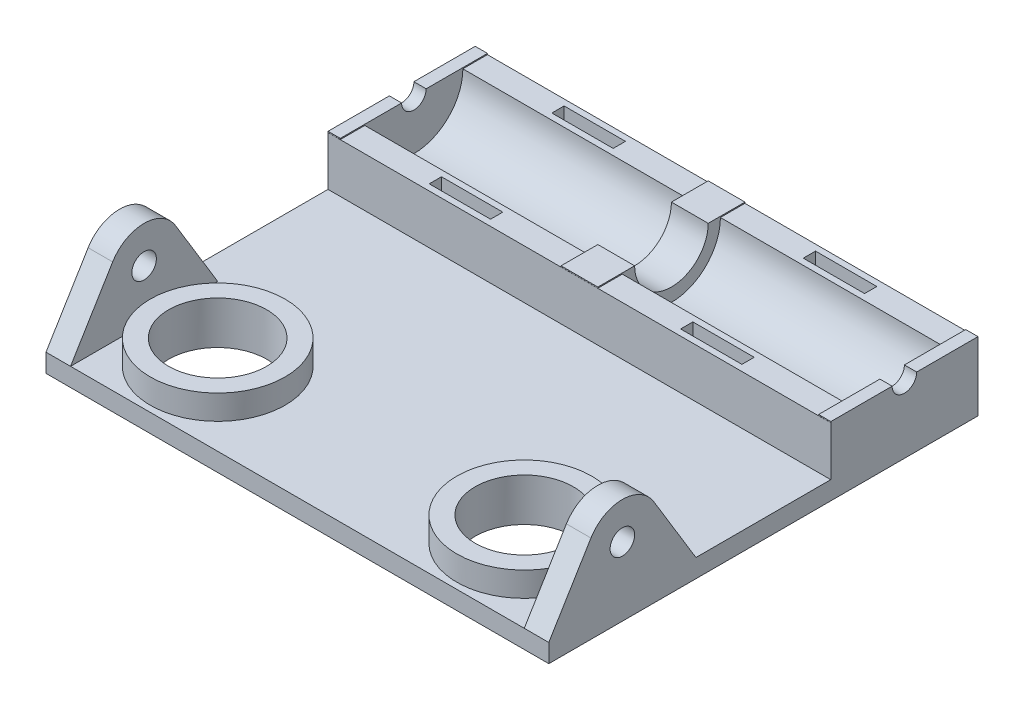
SolidWorks part; units mm, degrees
ref_plane "Front Plane" through (0, 0, 0) normal (0, 0, 1) x (1, 0, 0)
ref_plane "Top Plane" through (0, 0, 0) normal (0, 1, 0) x (1, 0, 0)
ref_plane "Right Plane" through (0, 0, 0) normal (1, 0, 0) x (0, 0, -1)
sketch "Sketch1" plane through (0, 0, 0) normal (0, 1, 0) x (1, 0, 0)
  line L1 (-20.5, -17.5) -> (20.5, -17.5)
  line L2 (-20.5, -17.5) -> (-20.5, 17.5)
  line L3 (-20.5, 17.5) -> (20.5, 17.5)
  line L4 (20.5, -17.5) -> (20.5, 17.5)
  line L5 (-20.5, -17.5) -> (20.5, 17.5) construction
  line L6 (-20.5, 17.5) -> (20.5, -17.5) construction
  point P0 (0, 0)
  dimension "D1" = 41
  dimension "D2" = 35
extrude "Boss-Extrude1" add sketch "Sketch1" along normal blind 1.5
sketch "Sketch2" plane through (20.5, 0, 0) normal (1, 0, 0) x (0, 0, -1)
  line L0 (15.5, 5.6) -> (17.5, 5.6)
  line L1 (17.5, 5.6) -> (17.5, 1.5)
  line L2 (7.5, 5.6) -> (5.5, 5.6)
  line L3 (5.5, 5.6) -> (5.5, 1.5)
  line L4 (-17.5, 1.5) -> (17.5, 1.5) construction
  line L5 (5.5, 1.5) -> (17.5, 1.5)
  arc A0 (7.5, 5.6) -> (15.5, 5.6) centre (11.5, 5.6) ccw
  dimension "D3" = 8
  dimension "D4" = 4.1
  dimension "D1" = 2
  dimension "D2" = 2
sketch "Sketch3" plane through (0, 0, 0) normal (1, 0, 0) x (0, 0, -1)
  line L0 (5.5, 1.5) -> (5.5, 5.6)
  line L1 (5.5, 5.6) -> (8.5, 5.6)
  line L2 (17.5, 5.6) -> (17.5, 1.5)
  line L3 (17.5, 1.5) -> (17.5, 0) construction
  line L4 (17.5, 1.5) -> (5.5, 1.5)
  line L5 (14.5, 5.6) -> (17.5, 5.6)
  arc A0 (8.5, 5.6) -> (14.5, 5.6) centre (11.5, 5.6) ccw
  dimension "D1" = 6
extrude "Boss-Extrude3" add sketch "Sketch3" along normal mid plane 3
sketch "Sketch4" plane through (-20.5, 0, 0) normal (-1, 0, 0) x (0, 0, 1)
  line L0 (-10.5, 5.6) -> (-5.5, 5.6)
  line L1 (-17.5, 5.6) -> (-12.5, 5.6)
  line L2 (-17.5, 5.6) -> (-17.5, 1.5)
  line L3 (-17.5, 1.5) -> (-5.5, 1.5)
  line L4 (-5.5, 5.6) -> (-5.5, 1.5)
  arc A0 (-12.5, 5.6) -> (-10.5, 5.6) centre (-11.5, 5.6) ccw
  dimension "D1" = 2
extrude "Boss-Extrude4" add sketch "Sketch4" against normal blind 1
mirror "Mirror1" about plane through (0, 0, 0) normal (1, 0, 0) of "Boss-Extrude4"
sketch "Sketch5" plane through (-20.5, 0, 0) normal (-1, 0, 0) x (0, 0, 1)
  line L0 (8.9359, 7.1573) -> (5.5, 1.5)
  line L1 (-5.5, 1.5) -> (17.5, 1.5) construction
  line L2 (14.0641, 7.1573) -> (17.5, 1.5)
  line L3 (5.5, 1.5) -> (17.5, 1.5)
  line L5 (-10.5, 5.6) -> (-5.5, 5.6) construction
  circle A0 centre (11.5, 5.6) radius 1
  arc A1 (14.0641, 7.1573) -> (8.9359, 7.1573) centre (11.5, 5.6) ccw
  dimension "D1" = 2
  dimension "D2" = 6
  dimension "D3" = 0
  dimension "D4" = 6
  dimension "D5" = 12
extrude "Boss-Extrude5" add sketch "Sketch5" against normal blind 2
mirror "Mirror2" about plane through (0, 0, 0) normal (1, 0, 0) of "Boss-Extrude5"
sketch "Sketch6" plane through (0, 1.5, 0) normal (0, 1, 0) x (1, 0, 0)
  line L0 (-18.5, -17.5) -> (18.5, -17.5) construction
  line L1 (-20.5, -17.5) -> (-20.5, -14.0641) construction
  line L2 (20.5, -17.5) -> (20.5, -14.0641) construction
  circle A0 centre (-12.5, -11.5) radius 4
  circle A1 centre (12.5, -11.5) radius 4
  dimension "D1" = 8
  dimension "D2" = 8
  dimension "D3" = 6
  dimension "D4" = 6
  dimension "D5" = 8
  dimension "D6" = 8
extrude "Cut-Extrude1" cut sketch "Sketch6" against normal blind 3
sketch "Sketch7" plane through (0, 1.5, 0) normal (0, 1, 0) x (1, 0, 0)
  circle A0 centre (12.5, -11.5) radius 4 construction
  circle A1 centre (-12.5, -11.5) radius 4 construction
  circle A2 centre (12.5, -11.5) radius 4
  circle A3 centre (-12.5, -11.5) radius 4
  circle A4 centre (-12.5, -11.5) radius 5.5
  circle A5 centre (12.5, -11.5) radius 5.5
  dimension "D1" = 1.5
  dimension "D2" = 1.5
extrude "Boss-Extrude6" add sketch "Sketch7" along normal blind 2
sketch "Sketch8" plane through (0, 5.6, 0) normal (0, 1, 0) x (1, 0, 0)
  line L1 (-12.75, 17) -> (-7.75, 17)
  line L2 (-12.75, 17) -> (-12.75, 16)
  line L3 (-12.75, 16) -> (-7.75, 16)
  line L4 (-7.75, 17) -> (-7.75, 16)
  line L5 (20.5, 11.5) -> (-21.9868, 11.5) construction
  line L6 (20.5, 5.5) -> (20.5, 17.5) construction
  line L7 (-7.75, 6) -> (-7.75, 7)
  line L8 (-12.75, 7) -> (-7.75, 7)
  line L9 (-12.75, 6) -> (-12.75, 7)
  line L10 (-12.75, 6) -> (-7.75, 6)
  line L11 (0, 18.4456) -> (0, 2.7509) construction
  line L12 (0, -55) -> (0, 55) construction
  line L13 (12.75, 6) -> (7.75, 6)
  line L14 (12.75, 6) -> (12.75, 7)
  line L15 (12.75, 7) -> (7.75, 7)
  line L16 (7.75, 6) -> (7.75, 7)
  line L17 (-22.5, 17.5) -> (22.5, 17.5) construction
  line L18 (-20.5, 12.5) -> (-20.5, 17.5) construction
  line L20 (7.75, 17) -> (7.75, 16)
  line L21 (12.75, 16) -> (7.75, 16)
  line L22 (12.75, 17) -> (12.75, 16)
  line L23 (12.75, 17) -> (7.75, 17)
  dimension "D1" = 1
  dimension "D2" = 5
  dimension "D3" = 7.75
  dimension "D4" = 0.5
sketch "Sketch9" plane through (0, 0, 0) normal (1, 0, 0) x (0, 0, -1)
  line L0 (15.4936, 5.5137) -> (17.4936, 5.5137)
  line L1 (17.4936, 5.5137) -> (17.4936, 1.4137)
  line L2 (7.4936, 5.5137) -> (5.4936, 5.5137)
  line L3 (5.4936, 5.5137) -> (5.4936, 1.4137)
  line L4 (5.4936, 1.4137) -> (17.4936, 1.4137)
  arc A0 (7.4936, 5.5137) -> (15.4936, 5.5137) centre (11.4936, 5.5137) ccw
  dimension "D3" = 8
  dimension "D1" = 2
  dimension "D2" = 2
extrude "Boss-Extrude7" add sketch "Sketch9" along normal mid plane 41
extrude "Cut-Extrude2" cut sketch "Sketch8" against normal blind 2
